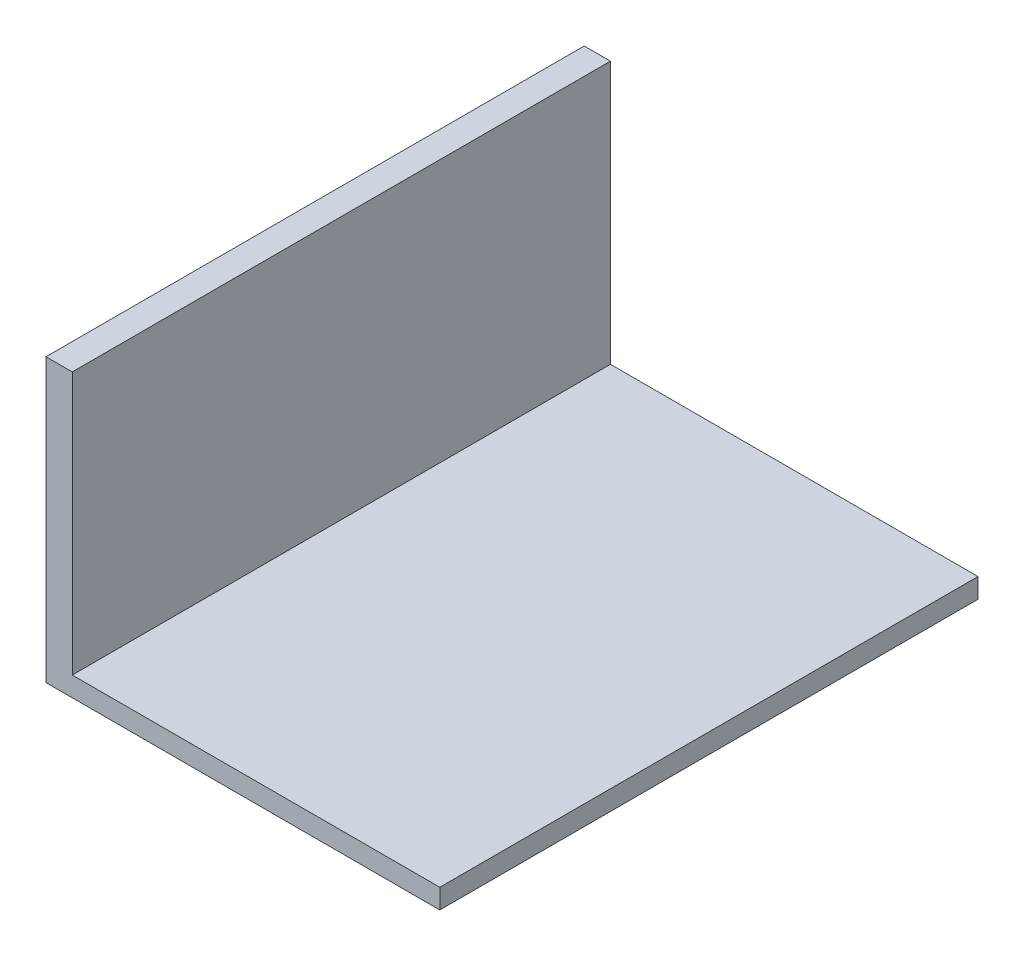
SolidWorks part; units mm, degrees
ref_plane "Front Plane" through (0, 0, 0) normal (0, 0, 1) x (1, 0, 0)
ref_plane "Top Plane" through (0, 0, 0) normal (0, 1, 0) x (1, 0, 0)
ref_plane "Right Plane" through (0, 0, 0) normal (1, 0, 0) x (0, 0, -1)
sketch "Sketch2" plane through (0, 0, 0) normal (0, 1, 0) x (1, 0, 0)
  line L1 (-75, -102.5) -> (75, -102.5)
  line L2 (-75, -102.5) -> (-75, 102.5)
  line L3 (-75, 102.5) -> (75, 102.5)
  line L4 (75, -102.5) -> (75, 102.5)
  line L5 (-75, -102.5) -> (75, 102.5) construction
  line L6 (-75, 102.5) -> (75, -102.5) construction
  point P0 (0, 0)
  dimension "D1" = 150
  dimension "D2" = 205
extrude "Boss-Extrude1" add sketch "Sketch2" along normal blind 7.5
sketch "Sketch3" plane through (0, 7.5, 0) normal (0, 1, 0) x (1, 0, 0)
  line L0 (-75, -102.5) -> (75, -102.5) construction
  line L1 (-75, 102.5) -> (-65, 102.5)
  line L2 (-75, 102.5) -> (-75, -102.5)
  line L3 (-75, -102.5) -> (-65, -102.5)
  line L4 (-65, 102.5) -> (-65, -102.5)
  dimension "D1" = 10
extrude "Boss-Extrude2" add sketch "Sketch3" along normal blind 100
